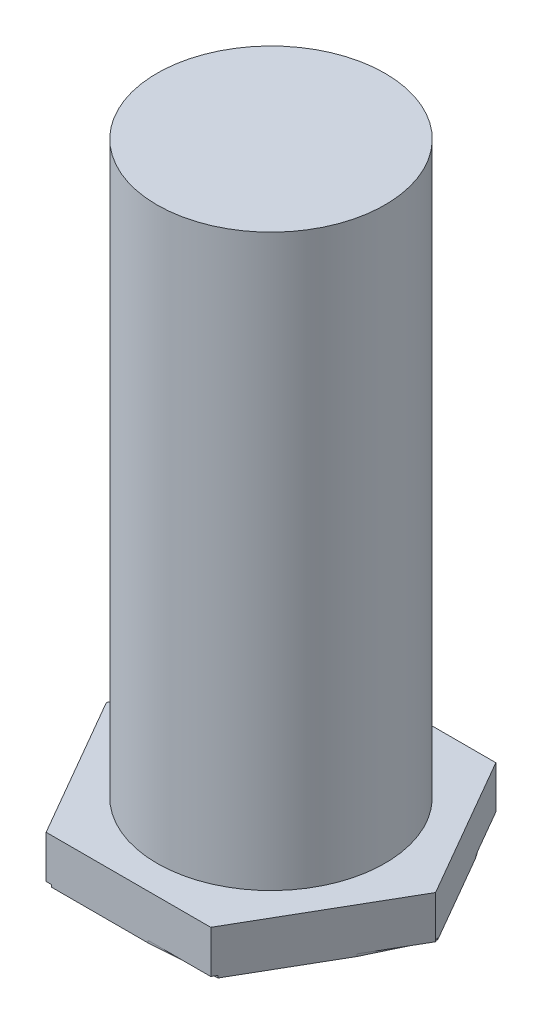
SolidWorks part; units mm, degrees
ref_plane "Front Plane" through (0, 0, 0) normal (0, 0, 1) x (1, 0, 0)
ref_plane "Top Plane" through (0, 0, 0) normal (0, 1, 0) x (1, 0, 0)
ref_plane "Right Plane" through (0, 0, 0) normal (1, 0, 0) x (0, 0, -1)
sketch "Sketch1" plane through (0, 0, 0) normal (0, 1, 0) x (1, 0, 0)
  circle A0 centre (0, 0) radius 5.08
  dimension "D1" = 10.16
extrude "Boss-Extrude1" add sketch "Sketch1" along normal blind 25.4
sketch "Sketch2" plane through (0, 0, 0) normal (0, -1, 0) x (1, 0, 0)
  line L1 (-7.3323, 0) -> (-3.6662, -6.35)
  line L2 (-3.6662, -6.35) -> (3.6662, -6.35)
  line L3 (3.6662, -6.35) -> (7.3323, 0)
  line L4 (7.3323, 0) -> (3.6662, 6.35)
  line L5 (3.6662, 6.35) -> (-3.6662, 6.35)
  line L6 (-3.6662, 6.35) -> (-7.3323, 0)
  circle A0 centre (0, 0) radius 6.35 construction
  dimension "D1" = 12.7
extrude "Boss-Extrude2" add sketch "Sketch2" along normal blind 2
sketch "Sketch3" plane through (0, -2, 0) normal (0, -1, 0) x (1, 0, 0)
  line L0 (-4.9796, 4.0751) -> (-3.4239, 6.35)
  line L1 (-3.6662, 6.35) -> (-7.3323, 0) construction
  line L2 (3.6662, 6.35) -> (-3.6662, 6.35) construction
  line L3 (0.8652, 6.35) -> (3.7869, 6.1408)
  line L4 (7.3323, 0) -> (3.6662, 6.35) construction
  line L5 (6.0526, 2.2166) -> (7.211, -0.2101)
  line L6 (3.6662, -6.35) -> (7.3323, 0) construction
  line L7 (4.9133, -4.1899) -> (3.4232, -6.35)
  line L8 (-3.6662, -6.35) -> (3.6662, -6.35) construction
  line L9 (-1.1474, -6.35) -> (-3.7876, -6.1397)
  line L10 (-7.3323, 0) -> (-3.6662, -6.35) construction
  line L11 (-6.0705, -2.1857) -> (-7.2109, 0.2103)
  line L12 (-6.0705, -2.1857) -> (-7.3323, 0)
  line L13 (-7.3323, 0) -> (-7.2109, 0.2103)
  line L14 (-3.7876, -6.1397) -> (-3.6662, -6.35)
  line L15 (-3.6662, -6.35) -> (-1.1474, -6.35)
  line L16 (4.9133, -4.1899) -> (3.6662, -6.35)
  line L17 (3.6662, -6.35) -> (3.4232, -6.35)
  line L18 (6.0526, 2.2166) -> (7.3323, 0)
  line L19 (7.211, -0.2101) -> (7.3323, 0)
  line L20 (0.8652, 6.35) -> (3.6662, 6.35)
  line L21 (3.6662, 6.35) -> (3.7869, 6.1408)
  line L22 (-3.4239, 6.35) -> (-3.6662, 6.35)
  line L23 (-3.6662, 6.35) -> (-4.9796, 4.0751)
  dimension "D1" = 0.2
  dimension "D2" = 0.2
  dimension "D3" = 0.2
  dimension "D4" = 0.2
  dimension "D5" = 0.2
  dimension "D6" = 0.2
extrude "Cut-Extrude1" cut sketch "Sketch3" against normal blind 0.1
